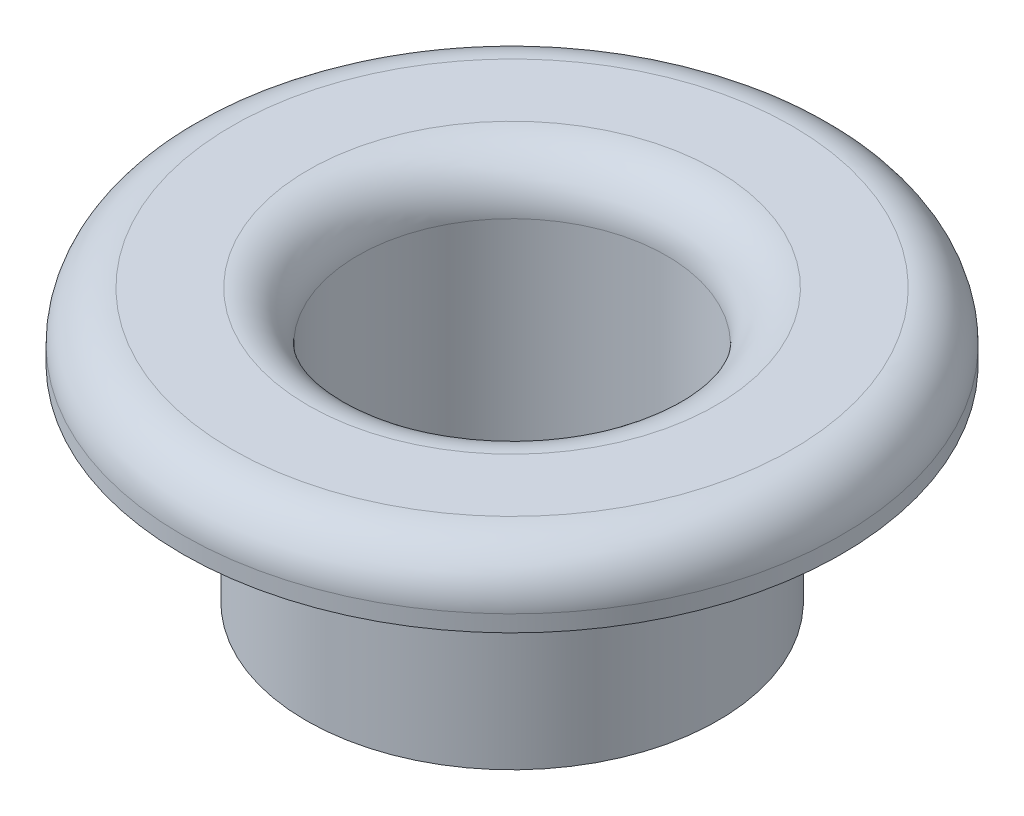
SolidWorks part; units mm, degrees
ref_plane "Front Plane" through (0, 0, 0) normal (0, 0, 1) x (1, 0, 0)
ref_plane "Top Plane" through (0, 0, 0) normal (0, 1, 0) x (1, 0, 0)
ref_plane "Right Plane" through (0, 0, 0) normal (1, 0, 0) x (0, 0, -1)
sketch "Sketch1" plane through (0, 0, 0) normal (0, 1, 0) x (1, 0, 0)
  circle A0 centre (0, 0) radius 2.3813
  circle A1 centre (0, 0) radius 3.175
  dimension "D1" = 4.7625
  dimension "D2" = 0.7937
extrude "Boss-Extrude1" add sketch "Sketch1" along normal blind 3.175
sketch "Sketch2" plane through (0, 3.175, 0) normal (0, 1, 0) x (1, 0, 0)
  circle A0 centre (0, 0) radius 5.08
  circle A1 centre (0, 0) radius 2.3813 construction
  circle A2 centre (0, 0) radius 2.3813
  dimension "D1" = 10.16
extrude "Boss-Extrude2" add sketch "Sketch2" along normal blind 1.016
fillet "Fillet1" radius 0.762 2 edges at (0, 4.191, 5.08) (0, 4.191, 2.3813)
ref_point "Point1"
